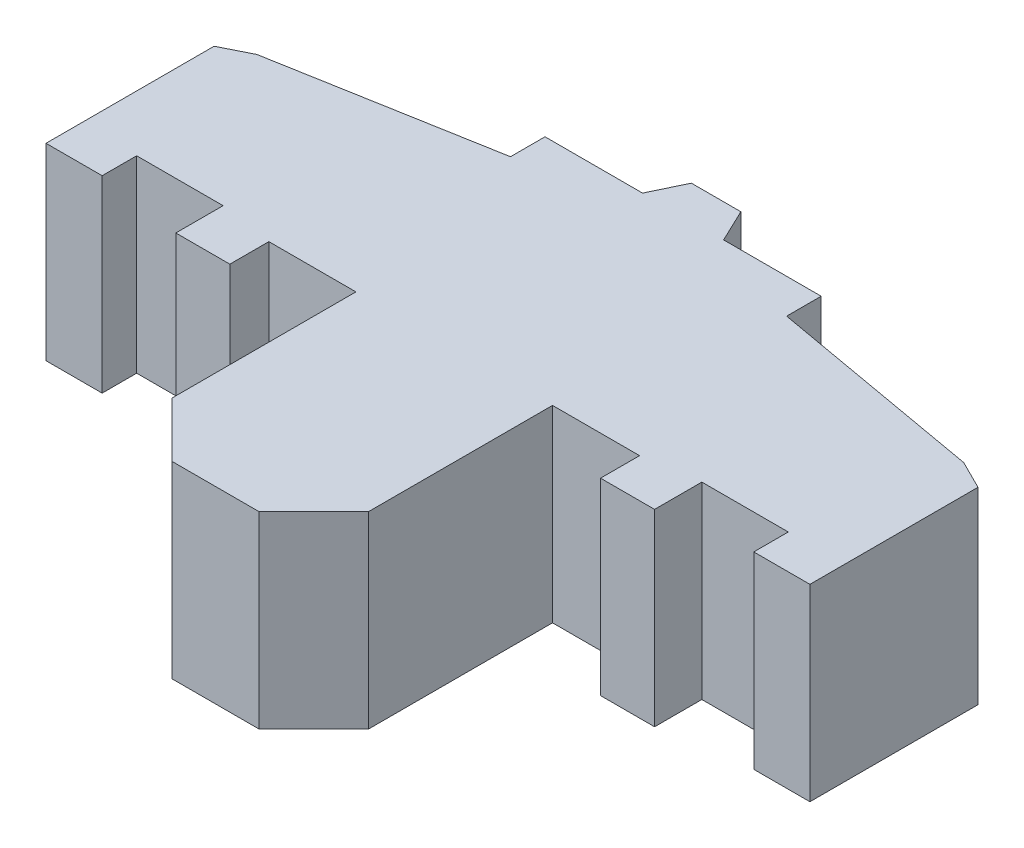
SolidWorks part; units mm, degrees
ref_plane "Front Plane" through (0, 0, 0) normal (0, 0, 1) x (1, 0, 0)
ref_plane "Top Plane" through (0, 0, 0) normal (0, 1, 0) x (1, 0, 0)
ref_plane "Right Plane" through (0, 0, 0) normal (1, 0, 0) x (0, 0, -1)
sketch "Sketch1" plane through (0, 0, 0) normal (0, 1, 0) x (1, 0, 0)
  line L0 (260.1107, 470.595) -> (1236.1824, 436.5098) construction
  line L1 (6.3745, 33.8499) -> (96.3745, 33.8499) construction
  line L2 (5.3663, 43.1982) -> (8.849, 44.9396)
  line L3 (12.2238, 26.8845) -> (22.7799, 26.8845)
  line L4 (5.3663, 43.1982) -> (5.3663, 22.6686)
  line L5 (5.3663, 22.6686) -> (10.2238, 22.6686)
  line L7 (8.849, 44.9396) -> (35.1527, 49.6138)
  line L8 (35.1527, 49.6138) -> (35.1527, 53.8297)
  line L9 (35.1527, 53.8297) -> (47.0672, 53.8297)
  line L10 (47.0672, 53.8297) -> (48.9919, 57.8623)
  line L11 (48.9919, 57.8623) -> (55.0408, 57.8623)
  line L12 (22.7799, 26.8845) -> (22.7799, 21.1105)
  line L13 (22.7799, 21.1105) -> (29.3787, 21.1105)
  line L14 (29.3787, 21.1105) -> (29.3787, 25.8763)
  line L15 (29.3787, 25.8763) -> (40.0101, 25.8763)
  line L16 (40.0101, 25.8763) -> (40.0101, 3.422)
  line L17 (40.0101, 3.422) -> (46.7143, -3.2822)
  line L18 (46.7143, -3.2822) -> (57.3183, -3.2822)
  line L19 (52.0163, 57.8623) -> (52.0163, -3.2822) construction
  line L20 (64.0225, 3.422) -> (57.3183, -3.2822)
  line L21 (64.0225, 25.8763) -> (64.0225, 3.422)
  line L22 (74.6539, 25.8763) -> (64.0225, 25.8763)
  line L23 (74.6539, 21.1105) -> (74.6539, 25.8763)
  line L24 (81.2528, 21.1105) -> (74.6539, 21.1105)
  line L25 (81.2528, 26.8845) -> (81.2528, 21.1105)
  line L26 (56.9654, 53.8297) -> (55.0408, 57.8623)
  line L27 (68.88, 53.8297) -> (56.9654, 53.8297)
  line L28 (68.88, 49.6138) -> (68.88, 53.8297)
  line L29 (95.1836, 44.9396) -> (68.88, 49.6138)
  line L31 (98.6663, 22.6686) -> (93.8089, 22.6686)
  line L32 (98.6663, 43.1982) -> (98.6663, 22.6686)
  line L33 (91.8089, 26.8845) -> (81.2528, 26.8845)
  line L34 (98.6663, 43.1982) -> (95.1836, 44.9396)
  line L36 (10.2238, 22.6686) -> (12.2238, 22.6686)
  line L39 (12.2238, 22.6686) -> (12.2238, 26.8845)
  line L40 (93.8089, 22.6686) -> (91.8089, 22.6686)
  line L43 (91.8089, 22.6686) -> (91.8089, 26.8845)
extrude "Boss-Extrude1" add sketch "Sketch1" along normal blind 23
